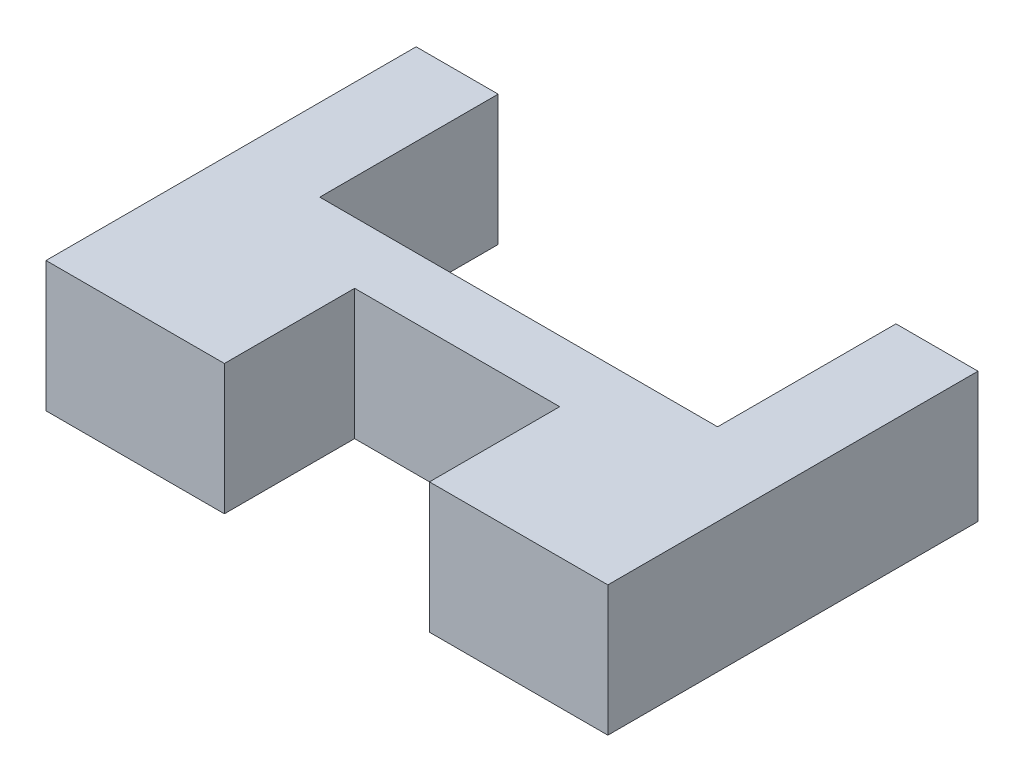
SolidWorks part; units mm, degrees
ref_plane "Front Plane" through (0, 0, 0) normal (0, 0, 1) x (1, 0, 0)
ref_plane "Top Plane" through (0, 0, 0) normal (0, 1, 0) x (1, 0, 0)
ref_plane "Right Plane" through (0, 0, 0) normal (1, 0, 0) x (0, 0, -1)
sketch "Sketch1" plane through (0, 0, 0) normal (0, 1, 0) x (1, 0, 0)
  line L0 (0, 0) -> (19.4, 0)
  line L1 (0, 0) -> (0, 8.7)
  line L2 (19.4, 0) -> (19.4, 8.7)
  line L3 (19.4, 8.7) -> (23.4, 8.7)
  line L4 (23.4, 8.7) -> (23.4, -9.35)
  line L5 (23.4, -9.35) -> (-4, -9.35)
  line L6 (9.7, 0) -> (9.7, 7.262) construction
  line L7 (-4, 8.7) -> (-4, -9.35)
  line L8 (0, 8.7) -> (-4, 8.7)
  point P11 (9.7, -9.35)
  dimension "D1" = 19.4
  dimension "D3" = 4
  dimension "D4" = 9.35
  dimension "D5" = 8.7
extrude "Boss-Extrude1" add sketch "Sketch1" along normal blind 6.35
sketch "Sketch2" plane through (0, 6.35, 0) normal (0, 1, 0) x (1, 0, 0)
  line L0 (9.7, 0) -> (9.7, -9.35) construction
  line L1 (19.4, 0) -> (0, 0) construction
  line L2 (-4, -9.35) -> (23.4, -9.35) construction
  line L3 (9.7, -9.35) -> (9.7, -3) construction
  line L4 (4.7, -9.35) -> (14.7, -9.35)
  line L5 (4.7, -9.35) -> (4.7, -3)
  line L6 (4.7, -3) -> (14.7, -3)
  line L7 (14.7, -9.35) -> (14.7, -3)
  dimension "D1" = 10
  dimension "D2" = 6.35
extrude "Cut-Extrude1" cut sketch "Sketch2" against normal up to next
